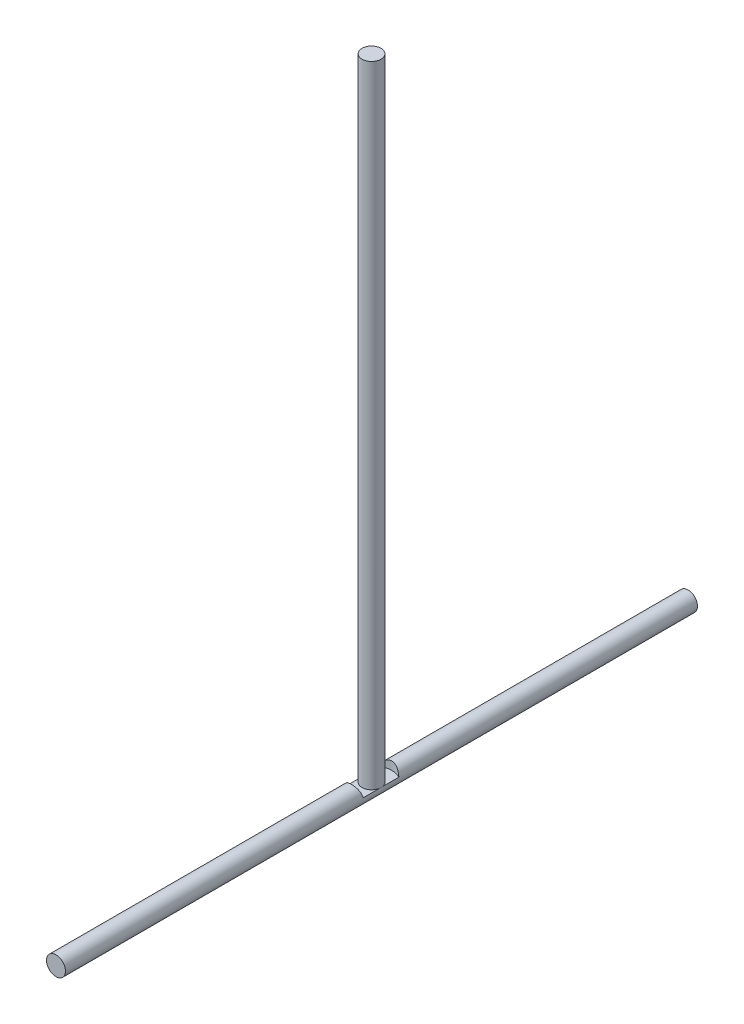
SolidWorks part; units mm, degrees
ref_plane "Front Plane" through (0, 0, 0) normal (0, 0, 1) x (1, 0, 0)
ref_plane "Top Plane" through (0, 0, 0) normal (0, 1, 0) x (1, 0, 0)
ref_plane "Right Plane" through (0, 0, 0) normal (1, 0, 0) x (0, 0, -1)
sketch "Sketch1" plane through (0, 0, 0) normal (0, 0, 1) x (1, 0, 0)
  circle A0 centre (0, 0) radius 7.5
  dimension "D1" = 15
extrude "Boss-Extrude1" add sketch "Sketch1" along normal blind 500
ref_plane "Plane1" through (0, 16, 0) normal (0, 1, 0) x (1, 0, 0)
sketch "Sketch2" plane through (0, 16, 0) normal (0, 1, 0) x (1, 0, 0)
  circle A0 centre (0, -250.3624) radius 16
  dimension "D1" = 32
extrude "Cut-Extrude1" cut sketch "Sketch2" against normal blind 15
sketch "Sketch4" plane through (0, 1, 0) normal (0, 1, 0) x (1, 0, 0)
  circle A0 centre (0, -250.3624) radius 7.5
  dimension "D1" = 15
extrude "Boss-Extrude2" add sketch "Sketch4" along normal blind 499
